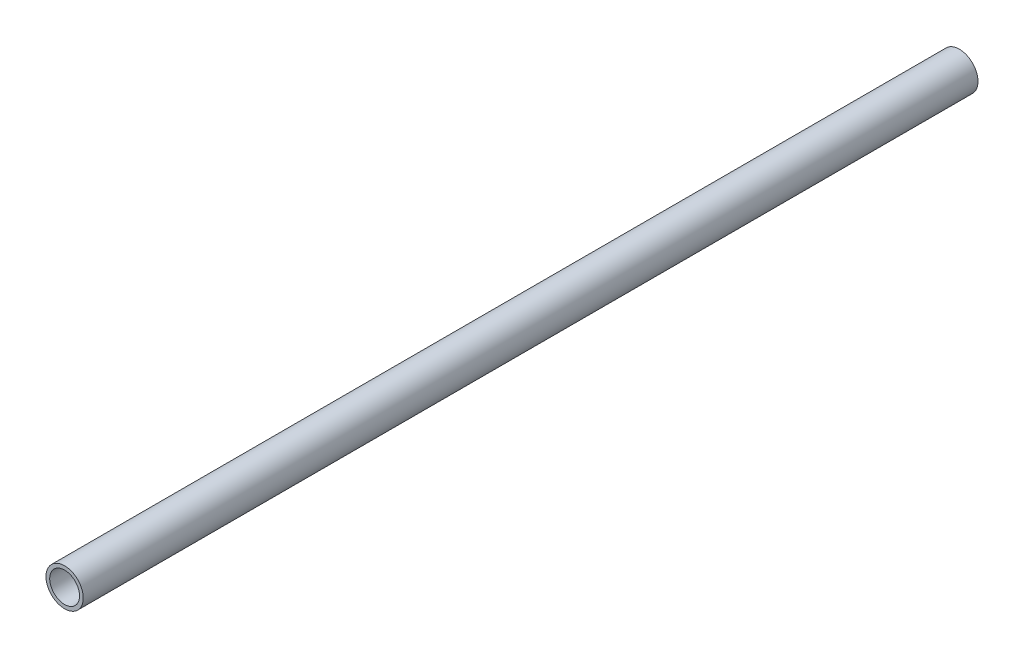
SolidWorks part; units mm, degrees
material "PVC Rigid"
ref_plane "Front Plane" through (0, 0, 0) normal (0, 0, 1) x (1, 0, 0)
ref_plane "Top Plane" through (0, 0, 0) normal (0, 1, 0) x (1, 0, 0)
ref_plane "Right Plane" through (0, 0, 0) normal (1, 0, 0) x (0, 0, -1)
sketch "Sketch1" plane through (0, 0, 0) normal (0, 0, 1) x (1, 0, 0)
  circle A0 centre (0, 0) radius 12.7
  circle A1 centre (0, 0) radius 10.16
  dimension "D1" = 25.4
  dimension "D2" = 20.32
extrude "Boss-Extrude1" add sketch "Sketch1" along normal blind 609.6
